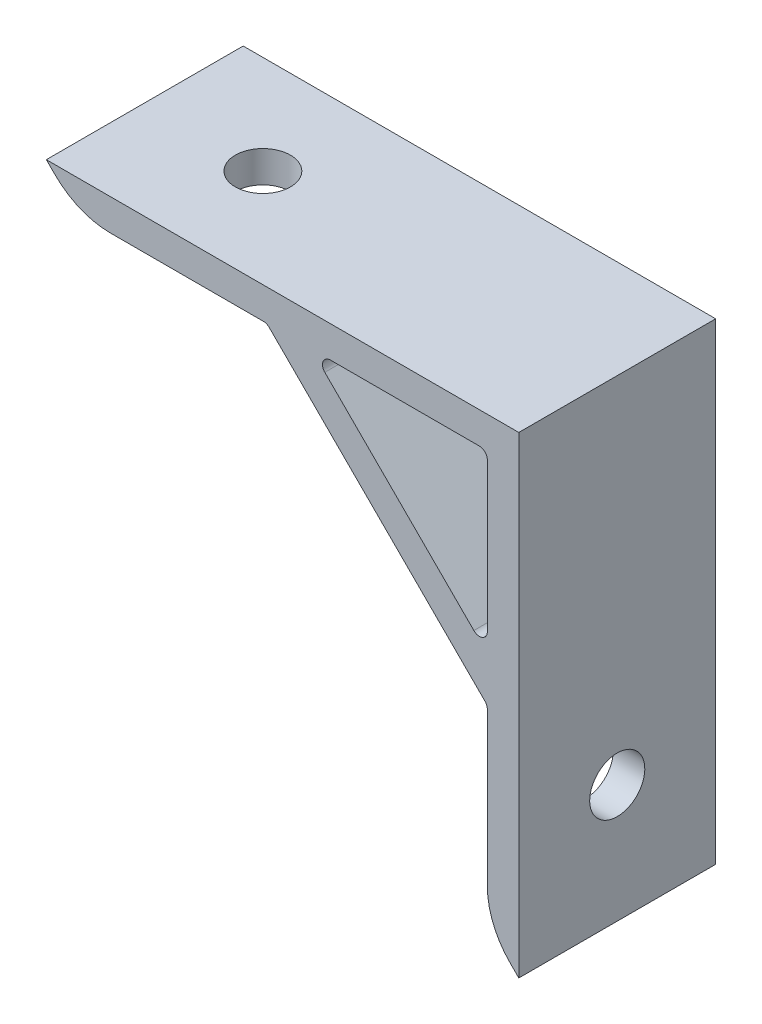
SolidWorks part; units mm, degrees
ref_plane "정면" through (0, 0, 0) normal (0, 0, 1) x (1, 0, 0)
ref_plane "윗면" through (0, 0, 0) normal (0, 1, 0) x (1, 0, 0)
ref_plane "우측면" through (0, 0, 0) normal (1, 0, 0) x (0, 0, -1)
sketch "스케치1" plane through (0, 0, 0) normal (0, 0, 1) x (1, 0, 0)
  line L0 (-30, 30) -> (30, 30)
  line L1 (30, 30) -> (30, -30)
  line L2 (-30, 30) -> (30, -30) construction
  line L3 (-26, 26) -> (-2, 26)
  line L4 (26, 26) -> (26, 3.6569)
  line L5 (-2, 26) -> (26, -2)
  line L6 (3.6569, 26) -> (26, 3.6569)
  line L7 (0.8284, 28.8284) -> (28.8284, 0.8284) construction
  line L8 (3.6569, 26) -> (26, 26)
  line L9 (-30, 26) -> (26, 26) construction
  line L10 (26, -2) -> (26, -26)
  line L11 (26, 26) -> (26, -30) construction
  line L12 (-30, 30) -> (-26, 26)
  line L13 (30, -30) -> (26, -26)
  point P2 (0, 0)
  dimension "D1" = 60
  dimension "D2" = 60
  dimension "D3" = 4
  dimension "D4" = 4
extrude "보스-돌출1" add sketch "스케치1" along normal blind 25
fillet "필렛1" radius 10 2 edges at (26, -26, 12.5) (-26, 26, 12.5)
fillet "필렛2" radius 1 5 edges at (26, 26, 12.5) (-2, 26, 12.5) (26, -2, 12.5) (26, 3.6569, 12.5) (3.6569, 26, 12.5)
sketch "스케치2" plane through (0, 30, 0) normal (0, 1, 0) x (1, 0, 0)
  line L0 (30, -25) -> (30, 0) construction
  line L1 (30, 0) -> (-30, 0) construction
  circle A0 centre (-15, -12.5) radius 3.5
  dimension "D3" = 7
  dimension "D1" = 45
  dimension "D2" = 12.5
extrude "컷-돌출2" cut sketch "스케치2" against normal blind 25
sketch "스케치4" plane through (30, 0, 0) normal (1, 0, 0) x (0, 0, -1)
  line L0 (0, -30) -> (0, 30) construction
  line L1 (-25, 30) -> (0, 30) construction
  circle A0 centre (-12.5, -15) radius 3.5
  point P4 (0, 0)
  point P6 (-9.8277, -23.2476)
  dimension "D1" = 7
  dimension "D2" = 12.5
  dimension "D3" = 45
extrude "컷-돌출3" cut sketch "스케치4" against normal blind 25
